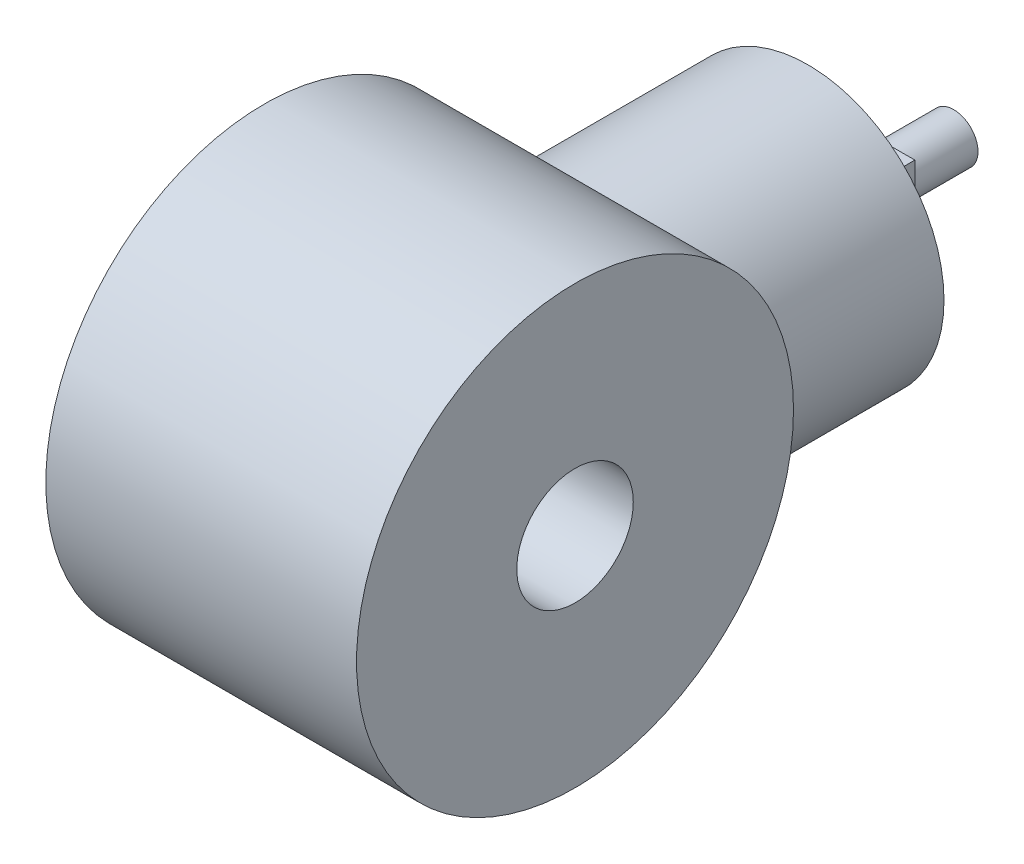
SolidWorks part; units mm, degrees
ref_plane "Front Plane" through (0, 0, 0) normal (0, 0, 1) x (1, 0, 0)
ref_plane "Top Plane" through (0, 0, 0) normal (0, 1, 0) x (1, 0, 0)
ref_plane "Right Plane" through (0, 0, 0) normal (1, 0, 0) x (0, 0, -1)
sketch "Sketch1" plane through (0, 0, 0) normal (1, 0, 0) x (0, 0, -1)
  line L0 (-25, 17.5) -> (-4.874, 21.9658)
  line L1 (-25, -17.5) -> (-25, 17.5)
  line L2 (-25, -17.5) -> (-4.874, -21.9658)
  circle A0 centre (0, 0) radius 6
  arc A1 (-4.874, -21.9658) -> (-4.874, 21.9658) centre (0, 0) ccw
  dimension "D1" = 12
  dimension "D3" = 35
sketch "Sketch2" plane through (0, 0, 0) normal (1, 0, 0) x (0, 0, -1)
  line L0 (-25, -17.5) -> (-4.874, -21.9658) construction
  line L1 (-25, 17.5) -> (-4.874, 21.9658) construction
  line L2 (-25, -17.5) -> (-25, 17.5) construction
  line L3 (-25, -17.5) -> (-4.874, -21.9658)
  line L4 (-25, 17.5) -> (-4.874, 21.9658)
  line L5 (-25, -17.5) -> (-25, 17.5)
  circle A0 centre (0, 0) radius 6 construction
  arc A1 (-4.874, -21.9658) -> (-4.874, 21.9658) centre (0, 0) ccw construction
  circle A2 centre (0, 0) radius 6
  arc A3 (-4.874, -21.9658) -> (-4.874, 21.9658) centre (0, 0) ccw
extrude "Boss-Extrude1" add sketch "Sketch2" along normal mid plane 32
sketch "Sketch3" plane through (0, 0, 0) normal (0, 0, 1) x (1, 0, 0)
  circle A0 centre (0, 0) radius 14
  dimension "D1" = 28
extrude "Boss-Extrude2" add sketch "Sketch3" against normal blind 40 contours A0
sketch "Sketch4" plane through (16, 0, 0) normal (1, 0, 0) x (0, 0, -1)
  circle A0 centre (0, 0) radius 6 construction
  circle A1 centre (0, 0) radius 6
extrude "Cut-Extrude1" cut sketch "Sketch4" against normal through all
sketch "Sketch5" plane through (0, 0, 0) normal (0, 1, 0) x (1, 0, 0)
  line L1 (-14, 40) -> (14, 40)
  line L2 (-14, 40) -> (-14, 70)
  line L3 (-14, 70) -> (14, 70)
  line L4 (14, 40) -> (14, 70)
  dimension "D1" = 30
extrude "Boss-Extrude3" add sketch "Sketch5" along normal mid plane 5
sketch "Sketch7" plane through (0, 0, -70) normal (0, 0, -1) x (-1, 0, 0)
  circle A0 centre (0, 0) radius 14
  circle A1 centre (0, 0) radius 15.2887
sketch "Sketch8" plane through (0, 0, -70) normal (0, 0, -1) x (-1, 0, 0)
  circle A0 centre (0, 0) radius 14 construction
  circle A1 centre (0, 0) radius 15.2887 construction
  circle A2 centre (0, 0) radius 14
  circle A3 centre (0, 0) radius 15.2887
extrude "Cut-Extrude2" cut sketch "Sketch8" against normal blind 35
sketch "Sketch9" plane through (0, 2.5, 0) normal (0, 1, 0) x (1, 0, 0)
  line L0 (13.775, 70) -> (-13.775, 70) construction
  circle A0 centre (-9, 62) radius 3
  circle A1 centre (9, 62) radius 3
  point P0 (0, 70)
  dimension "D1" = 6
extrude "Cut-Extrude3" cut sketch "Sketch9" against normal blind 35
sketch "Sketch10" plane through (16, 0, 0) normal (1, 0, 0) x (0, 0, -1)
  line L0 (-25, -17.5) -> (-4.874, -21.9658) construction
  line L1 (-25, 17.5) -> (-25, -17.5) construction
  line L2 (-4.874, 21.9658) -> (-25, 17.5) construction
  line L3 (-25, -17.5) -> (-4.874, -21.9658)
  line L4 (-25, 17.5) -> (-25, -17.5)
  line L5 (-4.874, 21.9658) -> (-25, 17.5)
  arc A2 (-4.874, 21.9658) -> (-4.874, -21.9658) centre (0, 0) ccw
extrude "Cut-Extrude4" cut sketch "Sketch10" against normal through all
sketch "Sketch11" plane through (0, 0, 0) normal (1, 0, 0) x (0, 0, -1)
  line L3 (40, 2.5) -> (40, -2.5)
  line L4 (70, -2.5) -> (70, 2.5) construction
  line L5 (70, -2.5) -> (40, -2.5) construction
  line L6 (70, 2.5) -> (40, 2.5) construction
  line L7 (70, -2.5) -> (70, 2.5)
  line L8 (70, -2.5) -> (40, -2.5)
  line L9 (70, 2.5) -> (40, 2.5)
extrude "Cut-Extrude5" cut sketch "Sketch11" against normal mid plane 30
sketch "Sketch13" plane through (0, 0, -40) normal (0, 0, -1) x (-1, 0, 0)
  circle A0 centre (0, 0) radius 2.5
  dimension "D1" = 5
sketch "Sketch14" plane through (0, 0, -40) normal (0, 0, -1) x (-1, 0, 0)
  circle A0 centre (0, 0) radius 2.5 construction
  circle A1 centre (0, 0) radius 2.5
extrude "Boss-Extrude4" add sketch "Sketch14" along normal blind 15
sketch "Sketch15" plane through (0, 0, -55) normal (0, 0, -1) x (-1, 0, 0)
  point P0 (0, 0)
sketch "Sketch17" plane through (0, 0, -40) normal (0, 0, -1) x (-1, 0, 0)
  line L1 (-6, -6) -> (6, -6)
  line L2 (-6, -6) -> (-6, 6)
  line L3 (-6, 6) -> (6, 6)
  line L4 (6, -6) -> (6, 6)
  line L5 (-6, -6) -> (6, 6) construction
  line L6 (-6, 6) -> (6, -6) construction
  point P0 (0, 0)
  dimension "D1" = 12
  dimension "D2" = 12
extrude "Boss-Extrude6" add sketch "Sketch17" along normal blind 5
